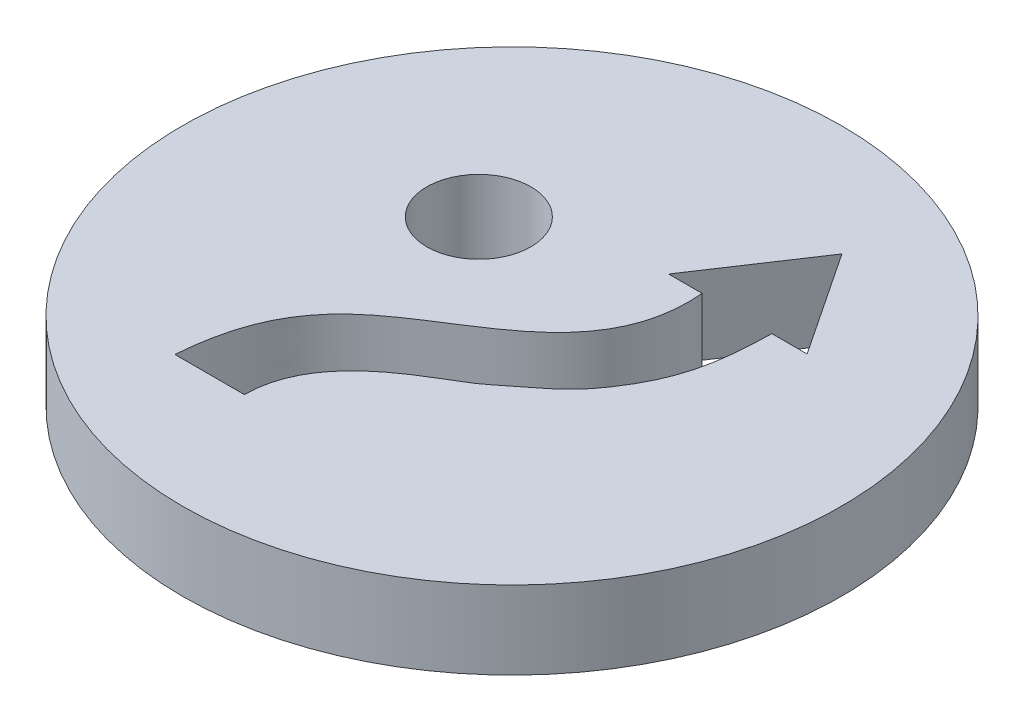
SolidWorks part; units mm, degrees
ref_plane "Front Plane" through (0, 0, 0) normal (0, 0, 1) x (1, 0, 0)
ref_plane "Top Plane" through (0, 0, 0) normal (0, 1, 0) x (1, 0, 0)
ref_plane "Right Plane" through (0, 0, 0) normal (1, 0, 0) x (0, 0, -1)
sketch "Sketch1" plane through (0, 0, 0) normal (0, 1, 0) x (1, 0, 0)
  line L0 (1.21, 3.3034) -> (2.1781, 3.3034)
  line L1 (5.2032, 3.3034) -> (3.2066, 6.3043)
  line L2 (3.2066, 6.3043) -> (1.21, 3.3034)
  line L4 (-3.8963, -5.8203) -> (-1.8963, -5.8203)
  line L5 (4.1867, 3.3034) -> (5.2032, 3.3034)
  circle A0 centre (0, 0) radius 9.5
  circle A1 centre (-2.9525, 1.9966) radius 1.5
  spline S0 degree 3 poles (2.1781, 3.3034) (2.4449, 0.1495) (-2.0856, -1.115) (-3.7581, -3.9543) (-3.8963, -5.8203) knots 0 0 0 0 0.630084 1 1 1 1
  spline S1 degree 3 poles (4.1867, 3.3034) (4.1623, 1.7166) (3.9166, 0.656) (2.6638, -1.102) (1.8224, -1.6783) (0.7353, -2.5932) (-1.8814, -3.7293) (-1.8963, -5.8203) knots 0 0 0 0 0.433165 0.505148 0.695982 0.747852 1 1 1 1
  point P11 (-2.9525, 1.9966)
  dimension "D1" = 3
  dimension "D2" = 19
  dimension "D3" = 1.21
  dimension "D4" = 1.3552
  dimension "D5" = 2.1781
  dimension "D6" = 3.0009
  dimension "D7" = 3.2066
  dimension "D8" = 4.1867
  dimension "D9" = 1.9966
  dimension "D10" = 1.8963
  dimension "D11" = 2.1297
  dimension "D12" = 2.9525
  dimension "D13" = 3.8963
  dimension "D14" = 3.3034
  dimension "D15" = 6.3043
  dimension "D16" = 0.6171
  dimension "D17" = 2.0692
  dimension "D18" = 5.8203
extrude "Boss-Extrude1" add sketch "Sketch1" along normal blind 2.25
